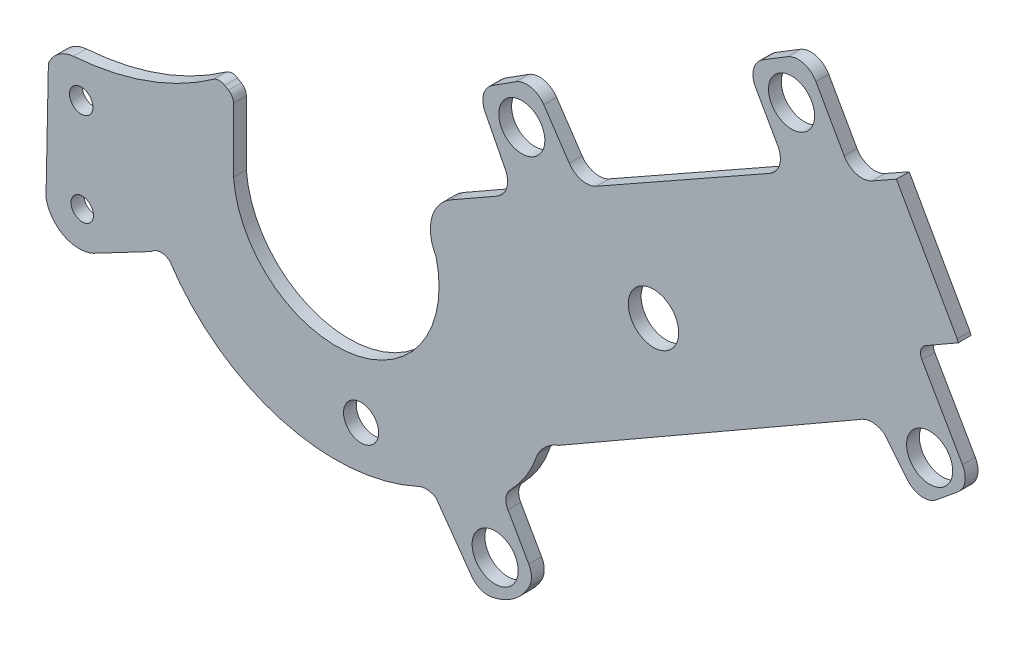
SolidWorks part; units mm, degrees
ref_plane "Plano frontal" through (0, 0, 0) normal (0, 0, 1) x (1, 0, 0)
ref_plane "Plano superior" through (0, 0, 0) normal (0, 1, 0) x (1, 0, 0)
ref_plane "Plano direito" through (0, 0, 0) normal (1, 0, 0) x (0, 0, -1)
sketch "Esboço1" plane through (0, 0, 0) normal (0, 0, 1) x (1, 0, 0)
  line L0 (341.3333, 723.5) -> (1706.6667, 723.5) construction
  line L1 (8592.0654, 5198.4757) -> (8473.4472, 5409.2245)
  line L2 (8473.4472, 5409.2245) -> (8425.9023, 5382.4642)
  line L3 (8371.4248, 5397.7027) -> (8316.4067, 5495.4534)
  line L4 (7814.8755, 5146.2863) -> (7784.8788, 5190.8972)
  line L5 (7814.8755, 5146.2863) -> (7834.7142, 5116.7822)
  line L6 (7887.5669, 5104.2662) -> (8226.5398, 5295.5591)
  line L7 (8241.7166, 5350.0537) -> (8198.4704, 5426.6865)
  line L8 (7730.1628, 5202.2939) -> (7684.4186, 5173.0939)
  line L9 (7670.3257, 5121.1686) -> (7709.8739, 5043.8158)
  line L10 (7694.0603, 4990.852) -> (7603.2452, 4939.1103)
  line L11 (8212.4493, 5480.4773) -> (8261.3755, 5510.3744)
  line L12 (7179.1129, 4765.424) -> (7179.1129, 4890.3985)
  line L13 (7169.4464, 4907.5221) -> (7161.8765, 4912.0904)
  line L14 (6817.6443, 4777.4402) -> (6812.9847, 4548.0416)
  line L15 (6905.4237, 4499.8206) -> (7018.7832, 4559.4231)
  line L16 (7574.5914, 4420.6905) -> (7643.8248, 4323.5375)
  line L17 (7755.6114, 4399.4593) -> (7714.8661, 4470.9739)
  line L18 (7814.8755, 4629.7982) -> (8402.0821, 4967.1323)
  line L19 (8449.6112, 4967.1323) -> (8495.0898, 4911.5417)
  line L20 (8551.3773, 4905.91) -> (8593.1164, 4940.0567)
  line L21 (8602.4689, 4990.9478) -> (8523.1587, 5128.9461)
  line L22 (8530.5331, 5156.2521) -> (8594.2385, 5192.8648)
  line L23 (8594.2385, 5192.8648) -> (8592.0654, 5198.4757)
  line L24 (8324.974, 5402.6954) -> (8212.4493, 5470.1098)
  arc A0 (7730.1628, 5202.2939) -> (7784.8788, 5190.8972) centre (7751.685, 5168.5775) cw
  arc A1 (7709.8739, 5043.8158) -> (7694.0603, 4990.852) centre (7674.2588, 5025.6068) cw
  arc A2 (7684.4186, 5173.0939) -> (7670.3257, 5121.1686) centre (7705.9408, 5139.3776) ccw
  arc A3 (7834.7142, 5116.7822) -> (7887.5669, 5104.2662) centre (7867.908, 5139.1019) ccw
  arc A4 (8226.5398, 5295.5591) -> (8241.7166, 5350.0537) centre (8206.8809, 5330.3948) ccw
  arc A5 (8316.4067, 5495.4534) -> (8261.3755, 5510.3744) centre (8281.5487, 5475.8339) ccw
  arc A6 (8425.9023, 5382.4642) -> (8371.4248, 5397.7027) centre (8406.2828, 5417.3222) cw
  arc A7 (7603.2452, 4939.1103) -> (7574.5913, 4828.9617) centre (7643.7756, 4869.7655) ccw
  arc A8 (7179.1129, 4765.424) -> (7574.5913, 4828.9617) centre (7379.4912, 4780.7664) ccw
  arc A9 (7139.9909, 4911.2932) -> (6866.7749, 4813.6202) centre (6828.5902, 5351.3958) cw
  arc A10 (6866.7749, 4813.6202) -> (6817.6443, 4777.4402) centre (6872.6378, 4754.2102) ccw
  arc A11 (6812.9847, 4548.0416) -> (6905.4237, 4499.8206) centre (6877.7187, 4559.4231) ccw
  arc A12 (7018.7832, 4559.4231) -> (7054.5279, 4561.4117) centre (7037.7196, 4541.2917) cw
  arc A13 (7054.5279, 4561.4117) -> (7539.8146, 4422.8313) centre (7377.6555, 4773.965) ccw
  arc A14 (7539.8146, 4422.8313) -> (7574.5914, 4420.6905) centre (7555.2159, 4389.4819) cw
  arc A15 (7684.1782, 4307.5147) -> (7756.11, 4360.7582) centre (7663.8135, 4410.2389) ccw
  arc A16 (7719.6333, 4506.9521) -> (7772.7809, 4593.562) centre (7562.0489, 4663.2644) ccw
  arc A17 (7772.7809, 4593.562) -> (7814.8755, 4629.7982) centre (7840.427, 4557.5476) cw
  arc A18 (7714.8661, 4470.9739) -> (7719.6333, 4506.9521) centre (7740.9323, 4485.825) cw
  arc A19 (7643.8248, 4323.5375) -> (7684.1782, 4307.5147) centre (7676.3997, 4346.7511) ccw
  arc A20 (7755.6114, 4399.4593) -> (7756.11, 4360.7582) centre (7720.8565, 4379.6578) cw
  arc A21 (7179.1129, 4890.3985) -> (7169.4464, 4907.5221) centre (7159.1129, 4890.3985) ccw
  arc A22 (7161.8765, 4912.0904) -> (7139.9909, 4911.2932) centre (7151.5429, 4894.9668) ccw
  arc A23 (8402.0821, 4967.1323) -> (8449.6112, 4967.1323) centre (8425.8466, 4933.2666) cw
  arc A24 (8523.1587, 5128.9461) -> (8530.5331, 5156.2521) centre (8540.4989, 5138.9118) cw
  arc A25 (8593.1164, 4940.0567) -> (8602.4689, 4990.9478) centre (8567.7885, 4971.0163) ccw
  arc A26 (8495.0898, 4911.5417) -> (8551.3773, 4905.91) centre (8526.0493, 4936.8696) ccw
  circle A27 centre (7999.1364, 4936.7365) radius 49.2273
  circle A28 centre (8538.3055, 4970.6405) radius 45.0272
  circle A29 centre (7428.1606, 4474.7961) radius 34.2897
  circle A30 centre (7689.9479, 4377.6653) radius 45
  circle A31 centre (6881.7273, 4746.2835) radius 22.9189
  circle A32 centre (6883.8151, 4563.9625) radius 21.9291
  circle A33 centre (7741.9897, 5131.4107) radius 45
  arc A34 (8198.4704, 5426.6865) -> (8212.4493, 5480.4773) centre (8233.3061, 5446.3453) cw
  circle A35 centre (8268.7117, 5436.4026) radius 45
  point P16 (7727.2769, 5009.777)
  point P19 (7653.7777, 5153.535)
  point P22 (7785.8491, 5238.7006)
  point P23 (7763.0849, 5223.3091)
  point P28 (8296.4715, 5530.8721)
  point P31 (8391.0443, 5362.8447)
  point P32 (7855.3536, 5086.0873)
  point P35 (8261.3755, 5315.218)
  point P68 (7656.4846, 4305.7723)
  point P71 (7764.9505, 4383.0676)
  point P74 (7179.1129, 4901.6887)
  point P77 (7150.526, 4918.94)
  point P87 (8513.1929, 5146.2863)
  point P90 (8619.3722, 4961.5365)
  point P93 (8520.4177, 4880.5821)
  point P110 (8179.4828, 5460.3327)
  dimension "D5" = 72.5424
  dimension "D4" = 92.8158
  dimension "D7" = 166.6274
  dimension "D11" = 40
  dimension "D12" = 40
  dimension "D13" = 95.9718
  dimension "D14" = 40
  dimension "D15" = 40
  dimension "D16" = 40
  dimension "D17" = 136.2648
  dimension "D19" = 229.446
  dimension "D20" = 128.0735
  dimension "D21" = 141.1123
  dimension "D23" = 30
  dimension "D24" = 40
  dimension "D25" = 20
  dimension "D27" = 111.8236
  dimension "D32" = 20
  dimension "D33" = 40
  dimension "D35" = 131.1736
  dimension "D34" = 40
  dimension "D1" = 241.8374
  dimension "D2" = 94.5586
  dimension "D3" = 192.8139
  dimension "D6" = 466.2131
  dimension "D8" = 157.1497
  dimension "D9" = 161.4573
  dimension "D10" = 142.7503
  dimension "D18" = 33.3888
  dimension "D22" = 133.1893
  dimension "D26" = 677.2044
  dimension "D28" = 127.8499
  dimension "D29" = 213.0881
  dimension "D30" = 93.477
  dimension "D31" = 6.0171
extrude "Ressalto-extrusão1" add sketch "Esboço1" along normal blind 25 contours A34 L7 A4 L6 A3 L5 L4 A0 L8 A2 L9 A1 L10 A7 A8 L12 A21 L13 A22 A9 A10 L14 A11 L15 A12 A13 A14 L16 A19 A15 A20 L17 A18 A16 A17 L18 A23 L19 A26 L20 A25 L21 A24 L22 L23 L1 L2 A6 L3 A5 L11
